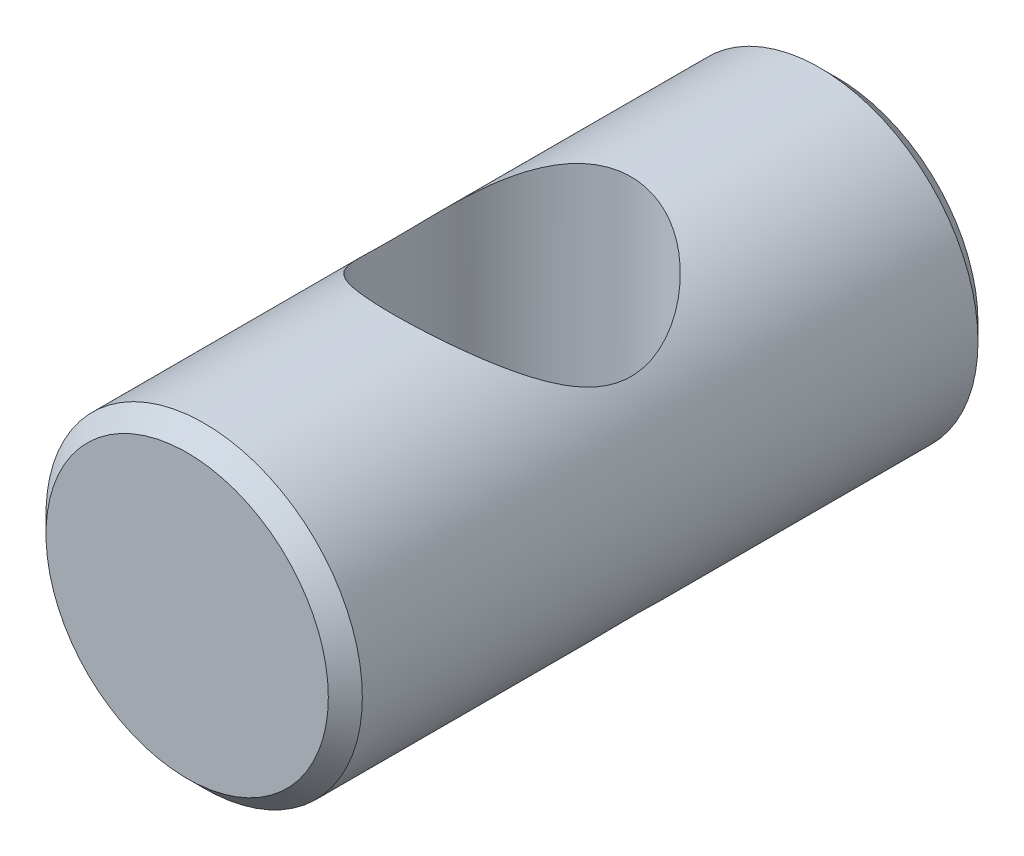
SolidWorks part; units mm, degrees
ref_plane "Front Plane" through (0, 0, 0) normal (0, 0, 1) x (1, 0, 0)
ref_plane "Top Plane" through (0, 0, 0) normal (0, 1, 0) x (1, 0, 0)
ref_plane "Right Plane" through (0, 0, 0) normal (1, 0, 0) x (0, 0, -1)
sketch "Sketch1" plane through (0, 0, 0) normal (0, 0, 1) x (1, 0, 0)
  circle A0 centre (0, 0) radius 4.65
  dimension "D1" = 9.3
extrude "Boss-Extrude1" add sketch "Sketch1" along normal blind 19.1
sketch "Sketch2" plane through (0, 0, 0) normal (0, 1, 0) x (1, 0, 0)
  circle A0 centre (0, -9.55) radius 3.5
extrude "Cut-Extrude1" cut sketch "Sketch2" against normal through all both and the other way through all
chamfer "Chamfer1" distance 0.5 angle 45 2 edges at (4.65, 0, 19.1) (4.65, 0, 0)
